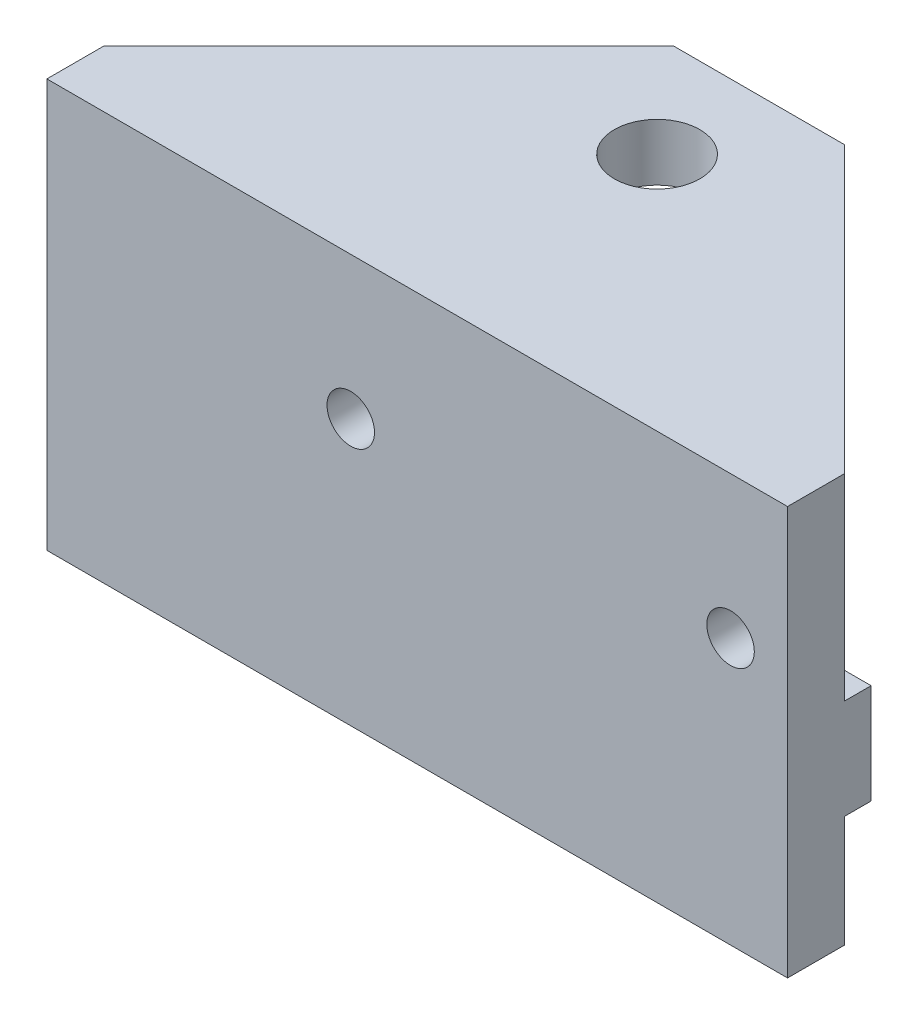
SolidWorks part; units mm, degrees
ref_plane "Plan de face" through (0, 0, 0) normal (0, 0, 1) x (1, 0, 0)
ref_plane "Plan de dessus" through (0, 0, 0) normal (0, 1, 0) x (1, 0, 0)
ref_plane "Plan de droite" through (0, 0, 0) normal (1, 0, 0) x (0, 0, -1)
sketch "Esquisse1" plane through (0, 0, 0) normal (0, 0, 1) x (1, 0, 0)
  line L1 (255.2385, 7.0289) -> (216.2385, 7.0289)
  line L2 (255.2385, 7.0289) -> (255.2385, -11.4711)
  line L3 (255.2385, -11.4711) -> (216.2385, -11.4711)
  line L4 (216.2385, 7.0289) -> (216.2385, -11.4711)
  line L5 (400, -11.4711) -> (0, -11.4711) construction
  line L7 (400, 7.0289) -> (0, 7.0289) construction
  line L8 (216.2385, -11.4711) -> (216.2385, 5.5289) construction
  line L9 (255.2385, -0.4711) -> (255.2385, -11.4711) construction
extrude "Boss.-Extru.1" add sketch "Esquisse1" along normal blind 3
sketch "Esquisse4" plane through (255.2385, 0, 0) normal (1, 0, 0) x (0, 0, -1)
  line L0 (0, -11.4711) -> (0, 7.0289) construction
  line L1 (0, -0.3411) -> (1.4, -0.3411)
  line L2 (0, -0.3411) -> (0, -5.6011)
  line L3 (0, -5.6011) -> (1.4, -5.6011)
  line L4 (1.4, -0.3411) -> (1.4, -5.6011)
  line L5 (0.508, -0.3411) -> (0.992, -0.3411) construction
  line L6 (0.992, -5.6011) -> (0.508, -5.6011) construction
  dimension "D1" = 1.4
extrude "Boss.-Extru.2" add sketch "Esquisse4" against normal up to surface (39 mm away) up to face at (216.2385, -2.2211, 1.5)
hole_wizard "Trou pour taraudage pour trou taraudé M31" positions "Esquisse6" profile "Esquisse5" hole size "M3" standard "Din"
sketch "Esquisse6" plane through (0, 0, 3) normal (0, 0, 1) x (1, 0, 0)
  point P0 (232.2385, 2.5289)
  point P3 (252.2385, 2.5289)
sketch "Esquisse5" plane through (232.2385, 2.5289, 3) normal (1, 0, 0) x (0, -1, 0)
  line L0 (0, 0) -> (0, 16)
  line L1 (0, 16) -> (1.25, 16)
  line L2 (1.25, 16) -> (1.25, 0)
  line L5 (1.25, 0) -> (0, 0)
  line L10 (0, 16) -> (-1.25, 16) construction
  line L11 (0, -6.35) -> (0, 107.95) construction
  dimension "Diamètre du perçage" = 2.5
  dimension "Profondeur du perçage" = 16
  dimension "Angle de pointe" = 180
sketch "Esquisse7" plane through (0, 7.0289, 0) normal (0, 1, 0) x (1, 0, 0)
  line L1 (216.2385, -3) -> (255.2385, -3)
  line L2 (216.2385, -3) -> (216.2385, 15)
  line L3 (216.2385, 15) -> (255.2385, 15)
  line L4 (255.2385, -3) -> (255.2385, 15)
  line L5 (255.2385, -3) -> (255.2385, 0) construction
  line L6 (255.2385, -3) -> (216.2385, -3) construction
  dimension "D1" = 18
extrude "Boss.-Extru.3" add sketch "Esquisse7" along normal blind 3
chamfer "Chanfrein1" distance 15 angle 45 2 edges at (216.2385, 8.5289, -15) (255.2385, 8.5289, -15)
hole_wizard "Dégagement M42" positions "Esquisse9" profile "Esquisse8" hole size "M4" standard "Din"
sketch "Esquisse9" plane through (0, 10.0289, 0) normal (0, 1, 0) x (1, 0, 0)
  line L0 (235.7385, 15) -> (235.7385, 9.63) construction
  line L1 (240.2385, 15) -> (231.2385, 15) construction
  line L2 (235.7385, 15) -> (235.7385, 9.63) construction
  line L6 (400, 12.63) -> (0, 12.63) construction
  point P0 (235.7385, 9.63)
  dimension "D1" = 3
sketch "Esquisse8" plane through (235.7385, 10.0289, -9.63) normal (1, 0, 0) x (0, 0, 1)
  line L0 (0, 0) -> (0, 16)
  line L1 (0, 16) -> (2.25, 16)
  line L2 (2.25, 16) -> (2.25, 0)
  line L5 (2.25, 0) -> (0, 0)
  line L10 (0, 16) -> (-2.25, 16) construction
  line L11 (0, -6.35) -> (0, 107.95) construction
  dimension "Diamètre du perçage" = 4.5
  dimension "Profondeur du perçage" = 16
  dimension "Angle de pointe" = 180
